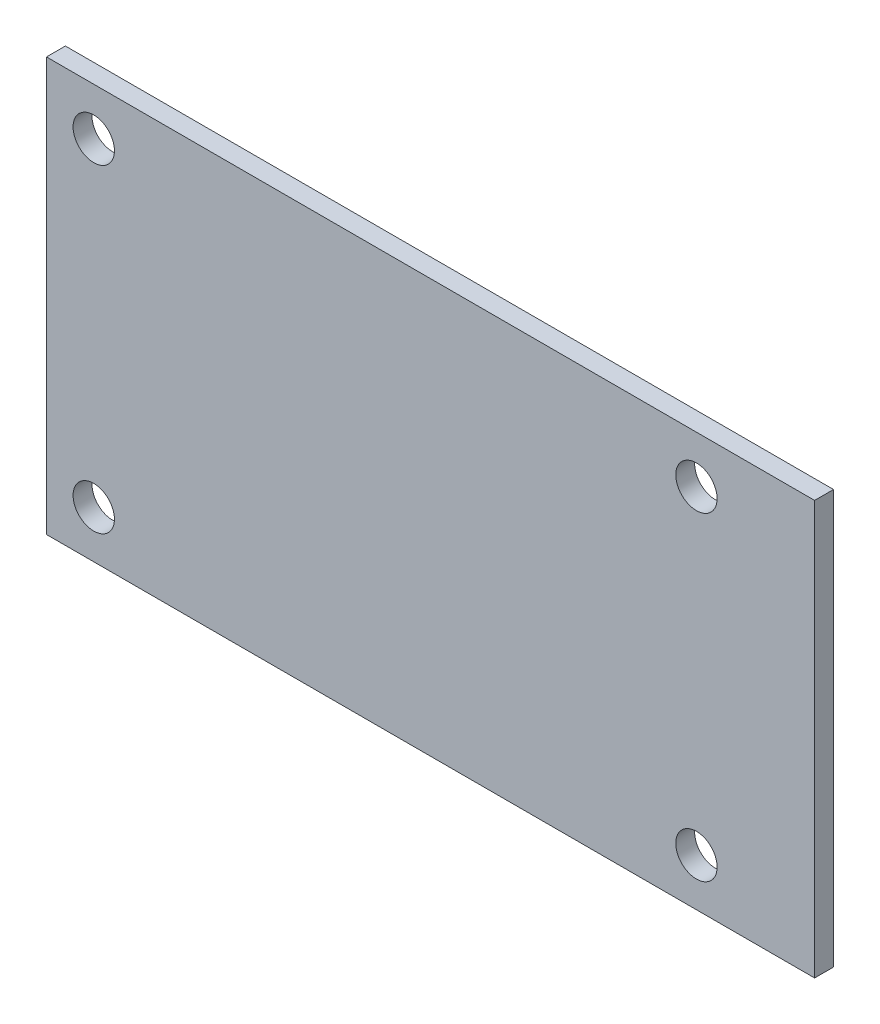
SolidWorks part; units mm, degrees
ref_plane "Front Plane" through (0, 0, 0) normal (0, 0, 1) x (1, 0, 0)
ref_plane "Top Plane" through (0, 0, 0) normal (0, 1, 0) x (1, 0, 0)
ref_plane "Right Plane" through (0, 0, 0) normal (1, 0, 0) x (0, 0, -1)
sketch "Sketch2" plane through (0, 0, 0) normal (0, 0, 1) x (1, 0, 0)
  line L1 (-32.5, 17.5) -> (32.5, 17.5)
  line L2 (-32.5, 17.5) -> (-32.5, -17.5)
  line L3 (-32.5, -17.5) -> (32.5, -17.5)
  line L4 (32.5, 17.5) -> (32.5, -17.5)
  line L5 (-32.5, 17.5) -> (32.5, -17.5) construction
  line L6 (-32.5, -17.5) -> (32.5, 17.5) construction
  point P0 (0, 0)
  dimension "D1" = 65
  dimension "D2" = 35
extrude "Boss-Extrude1" add sketch "Sketch2" along normal blind 1.6
sketch "Sketch3" plane through (0, 0, 1.6) normal (0, 0, 1) x (1, 0, 0)
  line L0 (-32.5, -17.5) -> (32.5, -17.5) construction
  line L1 (-28.5, 13.5) -> (22.5, 13.5) construction
  line L2 (-28.5, 13.5) -> (-28.5, -13.5) construction
  line L3 (-28.5, -13.5) -> (22.5, -13.5) construction
  line L4 (22.5, 13.5) -> (22.5, -13.5) construction
  line L5 (-32.5, 17.5) -> (-32.5, -17.5) construction
  circle A0 centre (-28.5, 13.5) radius 1.75
  circle A1 centre (-28.5, -13.5) radius 1.75
  circle A2 centre (22.5, 13.5) radius 1.75
  circle A3 centre (22.5, -13.5) radius 1.75
  point P2 (28.9242, 12.7625)
  point P8 (-28.1546, -11.2233)
  dimension "D1" = 3.5
  dimension "D2" = 4
  dimension "D3" = 4
  dimension "D4" = 31
  dimension "D5" = 55
extrude "Cut-Extrude1" cut sketch "Sketch3" against normal blind 1.6
